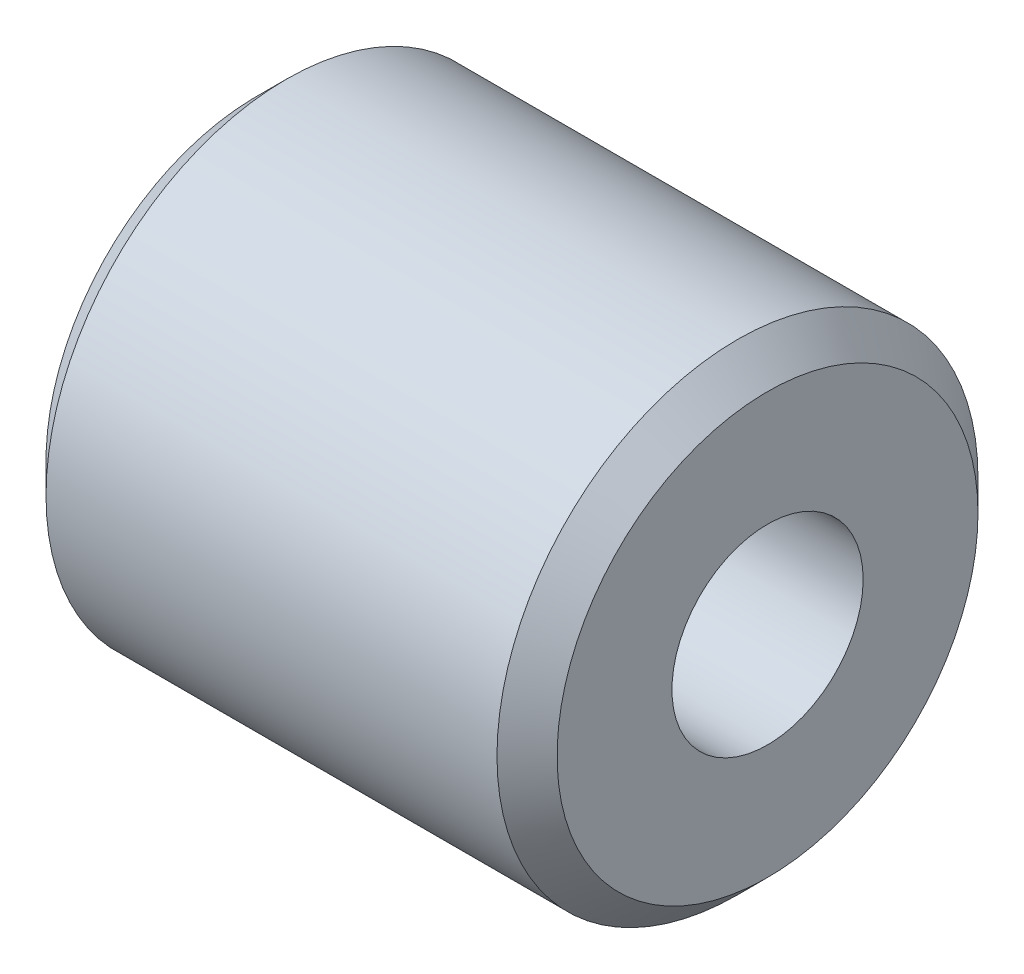
SolidWorks part; units mm, degrees
material "1023 Carbon Steel Sheet (SS)"
ref_plane "Front Plane" through (0, 0, 0) normal (0, 0, 1) x (1, 0, 0)
ref_plane "Top Plane" through (0, 0, 0) normal (0, 1, 0) x (1, 0, 0)
ref_plane "Right Plane" through (0, 0, 0) normal (1, 0, 0) x (0, 0, -1)
sketch "Sketch1" plane through (0, 0, 0) normal (1, 0, 0) x (0, 0, -1)
  circle A0 centre (0, 0) radius 1.59
  circle A1 centre (0, 0) radius 4
  dimension "D1" = 3.18
  dimension "D2" = 8
extrude "Boss-Extrude1" add sketch "Sketch1" along normal mid plane 8.5
chamfer "Chamfer1" distance 0.5 angle 45 2 edges at (-4.25, 0, -4) (4.25, 0, -4)
